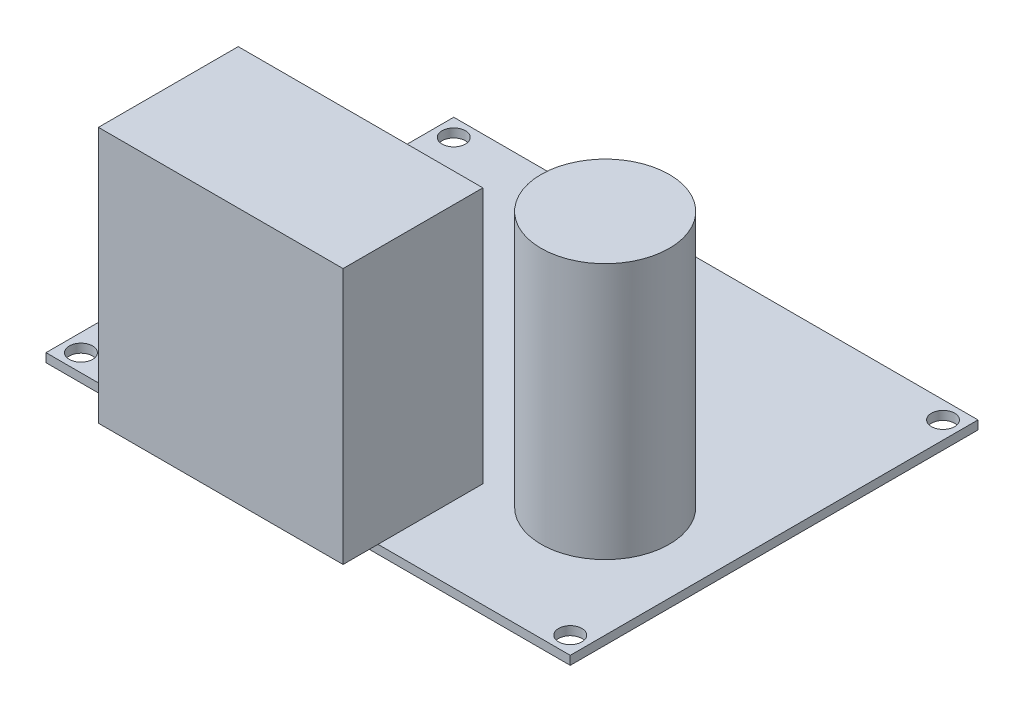
SolidWorks part; units mm, degrees
ref_plane "Plano frontal" through (0, 0, 0) normal (0, 0, 1) x (1, 0, 0)
ref_plane "Plano superior" through (0, 0, 0) normal (0, 1, 0) x (1, 0, 0)
ref_plane "Plano direito" through (0, 0, 0) normal (1, 0, 0) x (0, 0, -1)
sketch "Esboço1" plane through (0, 0, 0) normal (0, 1, 0) x (1, 0, 0)
  line L1 (0, 0) -> (90, 0)
  line L2 (0, 0) -> (0, 70)
  line L3 (0, 70) -> (90, 70)
  line L4 (90, 0) -> (90, 70)
  dimension "D1" = 90
  dimension "D2" = 70
extrude "Ressalto-extrusão1" add sketch "Esboço1" along normal blind 1.5
sketch "Esboço2" plane through (0, 1.5, 0) normal (0, 1, 0) x (1, 0, 0)
  line L0 (90, 0) -> (90, 70) construction
  line L1 (0, 70) -> (0, 0) construction
  line L2 (0, 0) -> (90, 0) construction
  line L3 (90, 70) -> (0, 70) construction
  circle A0 centre (87, 3) radius 2
  circle A1 centre (87, 67) radius 2
  circle A2 centre (3, 3) radius 2
  circle A3 centre (3, 67) radius 2
  dimension "D1" = 4
  dimension "D2" = 4
  dimension "D3" = 4
  dimension "D4" = 4
  dimension "D5" = 3
  dimension "D6" = 3
  dimension "D7" = 3
  dimension "D8" = 3
  dimension "D9" = 3
  dimension "D10" = 3
  dimension "D11" = 3
  dimension "D12" = 3
extrude "Corte-extrusão1" cut sketch "Esboço2" against normal blind 1.5
sketch "Esboço3" plane through (0, 1.5, 0) normal (0, 1, 0) x (1, 0, 0)
  line L0 (90, 0) -> (90, 70) construction
  line L1 (0, 0) -> (90, 0) construction
  line L8 (15, 0) -> (15, -6)
  line L9 (15, -6) -> (57, -6)
  line L10 (57, -6) -> (57, 0)
  line L11 (15, 18) -> (57, 18)
  line L12 (15, 18) -> (15, 0)
  line L13 (57, 18) -> (57, 0)
  circle A0 centre (71, 25) radius 11
  dimension "D1" = 22
  dimension "D2" = 19
  dimension "D3" = 25
  dimension "D4" = 18
  dimension "D6" = 6
extrude "Ressalto-extrusão2" add sketch "Esboço3" along normal blind 44
